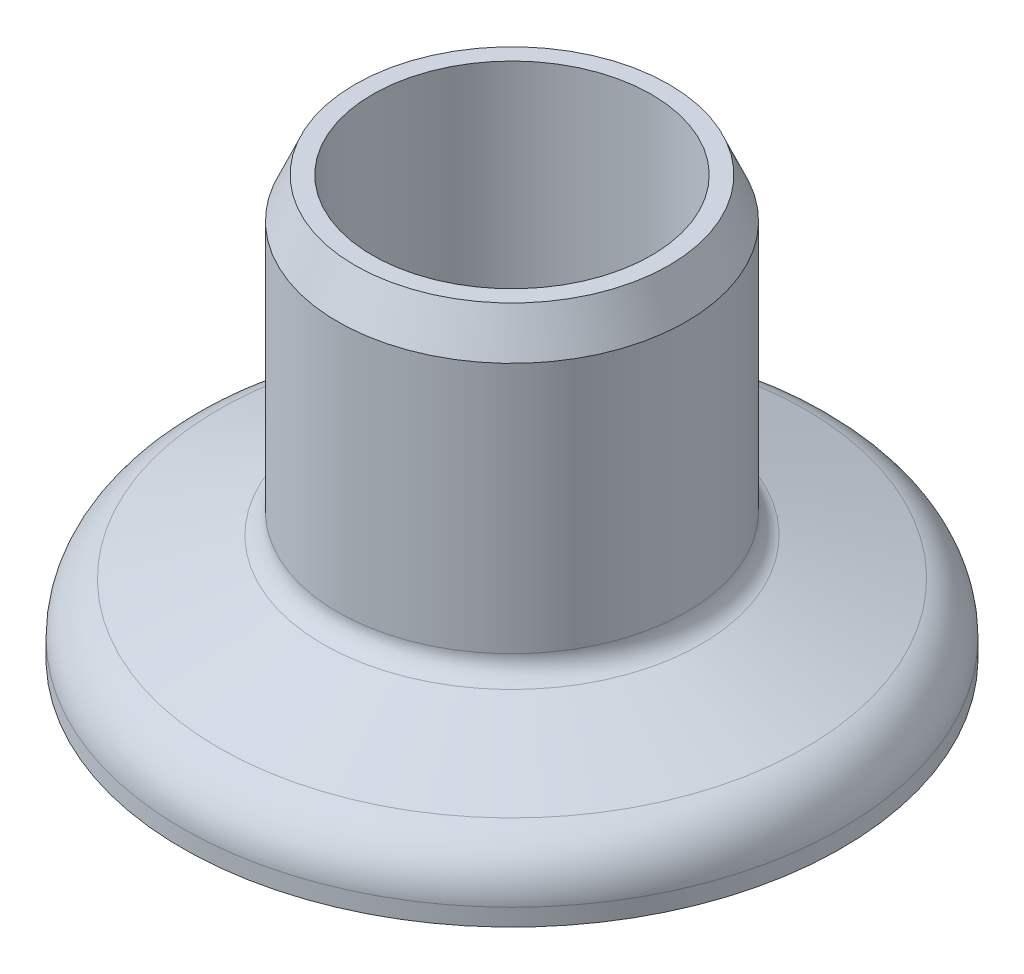
SolidWorks part; units mm, degrees
ref_plane "Front Plane" through (0, 0, 0) normal (0, 0, 1) x (1, 0, 0)
ref_plane "Top Plane" through (0, 0, 0) normal (0, 1, 0) x (1, 0, 0)
ref_plane "Right Plane" through (0, 0, 0) normal (1, 0, 0) x (0, 0, -1)
sketch "Sketch1" plane through (0, 0, 0) normal (0, 0, 1) x (1, 0, 0)
  line L1 (6.35, 19.05) -> (7.1437, 19.05)
  line L2 (0, -10.4775) -> (0, 10.4775) construction
  line L3 (7.9375, 17.231) -> (7.9375, 5.08)
  line L4 (7.9375, 5.08) -> (15, 2.54)
  line L5 (15, 2.54) -> (15, 0)
  line L6 (4.7575, 0) -> (-4.7575, 0) construction
  line L7 (15, 0) -> (6.35, 0)
  line L8 (7.1437, 19.05) -> (7.9375, 17.231)
  line L9 (6.35, 19.05) -> (6.35, 0)
  dimension "D1" = 7.9375
  dimension "D2" = 19.05
  dimension "D3" = 15
  dimension "D4" = 6.35
  dimension "D5" = 5.08
  dimension "D6" = 2.54
  dimension "D7" = 0.7938
  dimension "D8" = 1.819
ref_axis "Axis1" through (0, -0.9525, 0) along (0, 1, 0)
revolve "Revolve1" add sketch "Sketch1" angle 360 about axis through (0, -0.9525, 0) along (0, 1, 0)
fillet "Fillet1" radius 2.5 1 edges at (0, 2.54, -15)
fillet "Fillet2" radius 1 1 edges at (0, 5.08, -7.9375)
